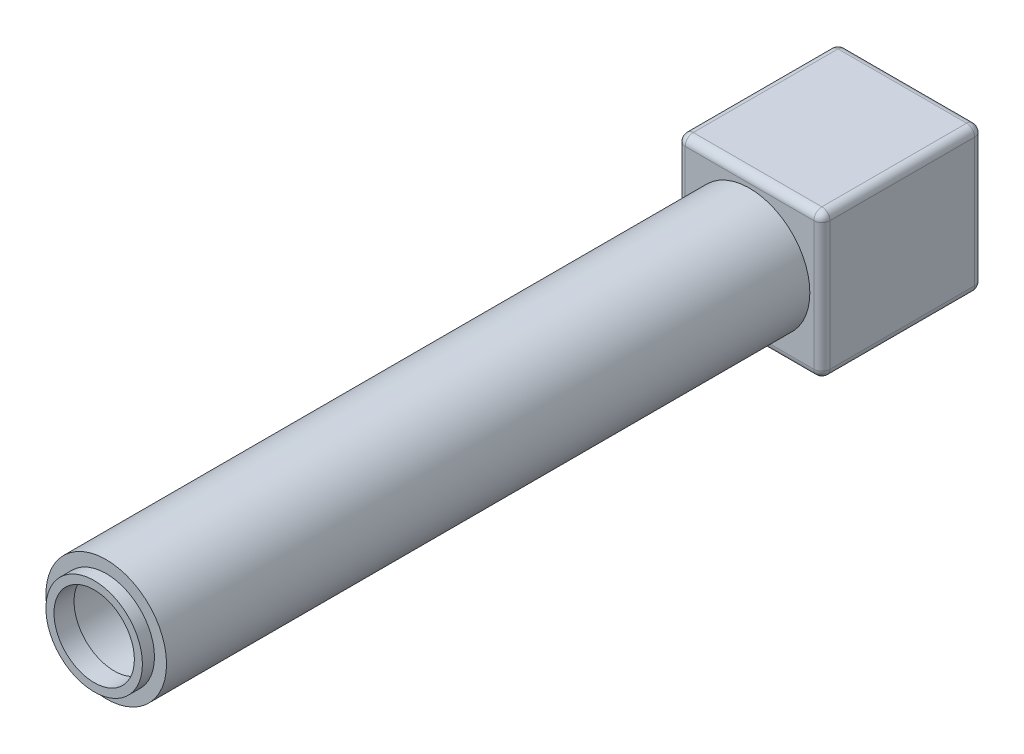
SolidWorks part; units mm, degrees
ref_plane "前视基准面" through (0, 0, 0) normal (0, 0, 1) x (1, 0, 0)
ref_plane "上视基准面" through (0, 0, 0) normal (0, 1, 0) x (1, 0, 0)
ref_plane "右视基准面" through (0, 0, 0) normal (1, 0, 0) x (0, 0, -1)
other "Configuration Table"
sketch "草图1" plane through (0, 0, 0) normal (0, 0, 1) x (1, 0, 0)
  circle A0 centre (0, 0) radius 7.5
  point P4 (0, 0)
extrude "凸台-拉伸1" add sketch "草图1" along normal blind 80
ref_plane "基准面2" through (0, 0, 80) normal (0, 0, 1) x (1, 0, 0)
shell "抽壳3" thickness 1.5
sketch "草图4" plane through (0, 0, 80) normal (0, 0, 1) x (1, 0, 0)
  line L1 (-12.5, -15) -> (12.5, -15) construction
  line L2 (-12.5, -15) -> (-12.5, 15) construction
  line L3 (-12.5, 15) -> (12.5, 15) construction
  line L4 (12.5, -15) -> (12.5, 15) construction
  line L5 (-12.5, -15) -> (12.5, 15) construction
  line L6 (-12.5, 15) -> (12.5, -15) construction
  circle A2 centre (0, 0) radius 5
  circle A3 centre (0, 0) radius 6 construction
  circle A4 centre (0, 0) radius 6
  point P0 (0, 0)
  dimension "D1" = 30
  dimension "D2" = 25
sketch "草图18" plane through (0, 0, 0) normal (0, 0, 1) x (1, 0, 0)
  line L1 (-9, -9) -> (9, -9)
  line L2 (-9, -9) -> (-9, 9)
  line L3 (-9, 9) -> (9, 9)
  line L4 (9, -9) -> (9, 9)
  line L5 (-9, -9) -> (9, 9) construction
  line L6 (-9, 9) -> (9, -9) construction
  point P0 (0, 0)
  dimension "D1" = 18
  dimension "D2" = 18
extrude "凸台-拉伸10" add sketch "草图18" against normal blind 20
ref_plane "基准面6" through (0, 0, -1.5) normal (0, 0, 1) x (1, 0, 0)
sketch "草图19" plane through (0, 0, -1.5) normal (0, 0, 1) x (1, 0, 0)
  line L1 (-7.5, 7.5) -> (7.5, 7.5)
  line L2 (-7.5, 7.5) -> (-7.5, -7.5)
  line L3 (-7.5, -7.5) -> (7.5, -7.5)
  line L4 (7.5, 7.5) -> (7.5, -7.5)
  line L5 (-7.5, 7.5) -> (7.5, -7.5) construction
  line L6 (-7.5, -7.5) -> (7.5, 7.5) construction
  point P0 (0, 0)
  dimension "D1" = 15
  dimension "D2" = 15
extrude "切除-拉伸5" cut sketch "草图19" against normal blind 17
ref_plane "基准面7" through (0, -9, 0) normal (0, -1, 0) x (-1, 0, 0)
sketch "草图22" plane through (0, -9, 0) normal (0, -1, 0) x (-1, 0, 0)
  line L0 (0, 0) -> (0, 20) construction
  line L1 (9, 0) -> (-9, 0) construction
  line L2 (9, 20) -> (-9, 20) construction
  circle A0 centre (0, 10) radius 7.5
  dimension "D2" = 15
  dimension "D1" = 20
extrude "切除-拉伸7" cut sketch "草图22" against normal blind 1.5
extrude "凸台-拉伸11" add sketch "草图4" along normal blind 1.5 and the other way blind 1 separate body
ref_plane "基准面8" through (0, 0, -1.5) normal (0, 0, -1) x (-1, 0, 0)
sketch "草图23" plane through (0, 0, -1.5) normal (0, 0, -1) x (-1, 0, 0)
  circle A1 centre (0, 0) radius 6
extrude "切除-拉伸8" cut sketch "草图23" against normal blind 3
fillet "圆角2" radius 1 12 edges at (0, -9, -20) (9, 0, -20) (9, -9, -10) (9, 0, 0) (0, 9, -20) (9, 9, -10) (0, 9, 0) (-9, -9, -10) (-9, 0, -20) (-9, 9, -10) (-9, 0, 0) (0, -9, 0)
